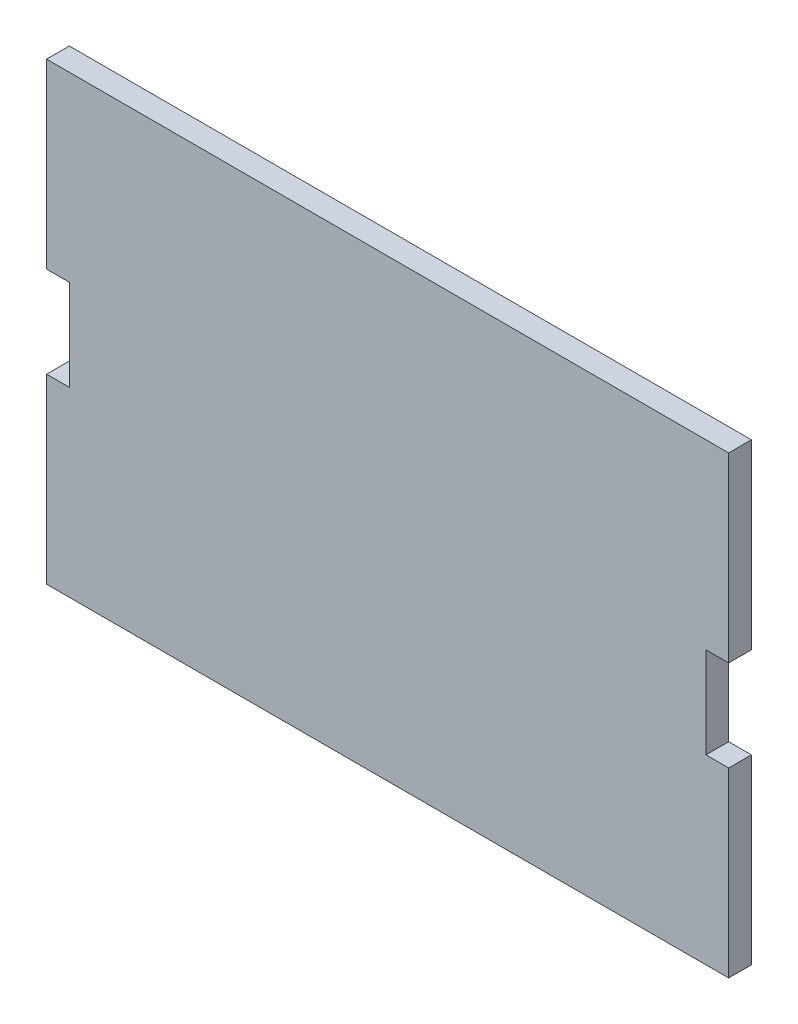
SolidWorks part; units mm, degrees
other "Veröffentlichte Referenzen"
other "Grundebene"
other "Verbindungsstück1"
other "Verbindungsstück2"
other "Verbindungsstück3"
other "Verbindungsstück4"
other "Verbindungsstück5"
other "Verbindungsstück6"
ref_plane "Ebene vorne" through (0, 0, 0) normal (0, 0, 1) x (1, 0, 0)
ref_plane "Ebene oben" through (0, 0, 0) normal (0, 1, 0) x (1, 0, 0)
ref_plane "Ebene rechts" through (0, 0, 0) normal (1, 0, 0) x (0, 0, -1)
sketch "Skizze1" plane through (0, 0, 0) normal (0, 0, 1) x (1, 0, 0)
  line L1 (-750, 0) -> (750, 0)
  line L2 (-750, 0) -> (-750, -1000)
  line L3 (-750, -1000) -> (750, -1000)
  line L4 (750, 0) -> (750, -1000)
  point P4 (0, 0)
  dimension "D2" = 1500
  dimension "L" = 1000
extrude "Aufsatz-Linear austragen1" add sketch "Skizze1" along normal blind 50
sketch "Skizze2" plane through (0, 0, 50) normal (0, 0, 1) x (1, 0, 0)
  line L0 (-750, 0) -> (-750, -1000) construction
  line L1 (-750, -400) -> (-700, -400)
  line L2 (-750, -400) -> (-750, -600)
  line L3 (-750, -600) -> (-700, -600)
  line L4 (-700, -400) -> (-700, -600)
  line L5 (750, 0) -> (-750, 0) construction
  dimension "D1" = 400
  dimension "D2" = 200
  dimension "D3" = 50
extrude "Schnitt-Linear austragen1" cut sketch "Skizze2" against normal up to next
sketch "Skizze3" plane through (0, 0, 50) normal (0, 0, 1) x (1, 0, 0)
  line L0 (750, -1000) -> (750, 0) construction
  line L1 (750, -400) -> (700, -400)
  line L2 (750, -400) -> (750, -600)
  line L3 (750, -600) -> (700, -600)
  line L4 (700, -400) -> (700, -600)
  line L5 (750, 0) -> (-750, 0) construction
  dimension "D1" = 50
  dimension "D2" = 200
  dimension "D3" = 400
extrude "Schnitt-Linear austragen2" cut sketch "Skizze3" against normal up to next
pattern_linear "Lineares Muster1" [suppressed] count 2 spacing 1000
sketch "Skizze4" plane through (0, 0, 50) normal (0, 0, 1) x (1, 0, 0)
  line L0 (750, 0) -> (-750, 0) construction
  line L1 (750, -1400) -> (700, -1400)
  line L2 (750, -1400) -> (750, -1600)
  line L3 (750, -1600) -> (700, -1600)
  line L4 (700, -1400) -> (700, -1600)
  line L6 (750, -1000) -> (750, -600) construction
  dimension "D1" = 200
  dimension "D2" = 50
  dimension "D3" = 1400
extrude "Schnitt-Linear austragen3" [suppressed] cut sketch "Skizze4" against normal up to next
sketch "Skizze5" [suppressed] plane through (0, 0, 50) normal (0, 0, 1) x (1, 0, 0)
  line L0 (750, -2000) -> (750, -1600) construction
  line L1 (750, -2400) -> (700, -2400)
  line L2 (750, -2400) -> (750, -2600)
  line L3 (750, -2600) -> (700, -2600)
  line L4 (700, -2400) -> (700, -2600)
  line L5 (750, -1400) -> (700, -1400) construction
  dimension "D1" = 200
  dimension "D2" = 50
  dimension "D3" = 1000
extrude "Schnitt-Linear austragen4" [suppressed] cut sketch "Skizze5" against normal up to next
